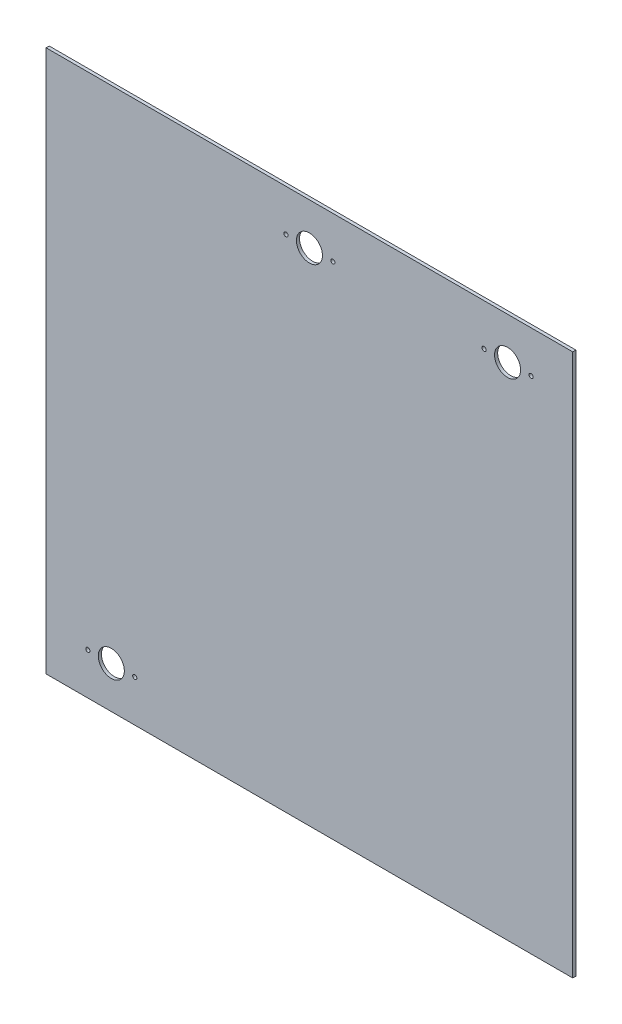
SolidWorks part; units mm, degrees
ref_plane "Přední rovina" through (0, 0, 0) normal (0, 0, 1) x (1, 0, 0)
ref_plane "Horní rovina" through (0, 0, 0) normal (0, 1, 0) x (1, 0, 0)
ref_plane "Pravá rovina" through (0, 0, 0) normal (1, 0, 0) x (0, 0, -1)
sketch "Skica1" plane through (0, 0, 0) normal (0, 0, 1) x (1, 0, 0)
  line L1 (-252.5, 260) -> (252.5, 260)
  line L2 (-252.5, 260) -> (-252.5, -260)
  line L3 (-252.5, -260) -> (252.5, -260)
  line L4 (252.5, 260) -> (252.5, -260)
  line L5 (-252.5, 260) -> (252.5, -260) construction
  line L6 (-252.5, -260) -> (252.5, 260) construction
  circle A0 centre (-212.5, -220) radius 2
  circle A1 centre (-190, -220) radius 12.5
  circle A2 centre (-167.5, -220) radius 2
  circle A3 centre (-22.5, 220) radius 2
  circle A4 centre (0, 220) radius 12.5
  circle A5 centre (22.5, 220) radius 2
  circle A6 centre (167.5, 220) radius 2
  circle A7 centre (190, 220) radius 12.5
  circle A8 centre (212.5, 220) radius 2
  point P0 (0, 0)
  dimension "D3" = 4
  dimension "D4" = 25
  dimension "D5" = 22.5
  dimension "D6" = 22.5
  dimension "D7" = 22.5
  dimension "D8" = 22.5
  dimension "D9" = 22.5
  dimension "D10" = 22.5
  dimension "D11" = 40
  dimension "D12" = 40
  dimension "D13" = 252.5
  dimension "D14" = 40
  dimension "D15" = 40
  dimension "D16" = 40
  dimension "D1" = 505
  dimension "D2" = 520
extrude "Přidat vysunutím1" add sketch "Skica1" along normal blind 3
